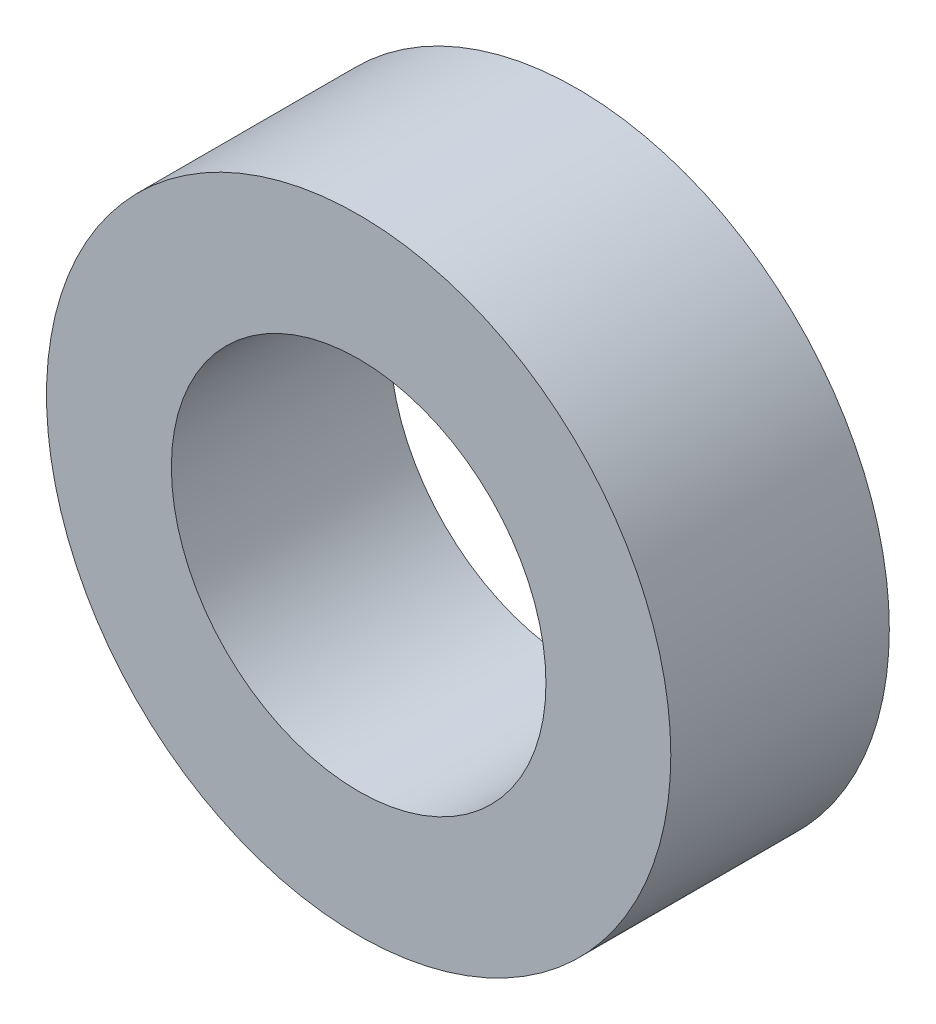
SolidWorks part; units mm, degrees
ref_plane "Plan de face" through (0, 0, 0) normal (0, 0, 1) x (1, 0, 0)
ref_plane "Plan de dessus" through (0, 0, 0) normal (0, 1, 0) x (1, 0, 0)
ref_plane "Plan de droite" through (0, 0, 0) normal (1, 0, 0) x (0, 0, -1)
sketch "Esquisse1" plane through (0, 0, 0) normal (0, 0, 1) x (1, 0, 0)
  circle A0 centre (0, 0) radius 10
  circle A1 centre (0, 0) radius 6
  dimension "D1" = 12
  dimension "D2" = 20
extrude "Boss.-Extru.1" add sketch "Esquisse1" along normal blind 7
